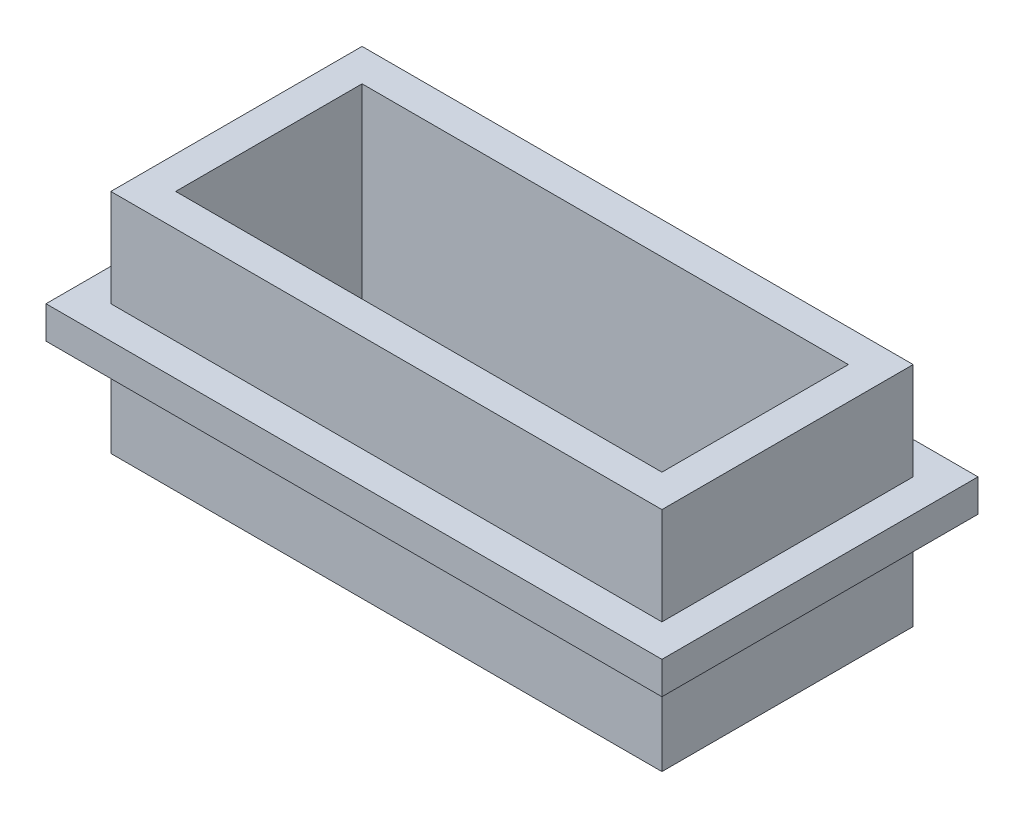
SolidWorks part; units mm, degrees
material "ABS"
ref_plane "Front Plane" through (0, 0, 0) normal (0, 0, 1) x (1, 0, 0)
ref_plane "Top Plane" through (0, 0, 0) normal (0, 1, 0) x (1, 0, 0)
ref_plane "Right Plane" through (0, 0, 0) normal (1, 0, 0) x (0, 0, -1)
sketch "Sketch1" plane through (0, 0, 0) normal (0, 1, 0) x (1, 0, 0)
  line L1 (-19.05, 7.3025) -> (19.05, 7.3025)
  line L2 (-19.05, 7.3025) -> (-19.05, -7.3025)
  line L3 (-19.05, -7.3025) -> (19.05, -7.3025)
  line L4 (19.05, 7.3025) -> (19.05, -7.3025)
  line L5 (-19.05, 7.3025) -> (19.05, -7.3025) construction
  line L6 (-19.05, -7.3025) -> (19.05, 7.3025) construction
  line L7 (-21.59, 9.8425) -> (21.59, 9.8425)
  line L8 (-21.59, 9.8425) -> (-21.59, -9.8425)
  line L9 (-21.59, -9.8425) -> (21.59, -9.8425)
  line L10 (21.59, 9.8425) -> (21.59, -9.8425)
  line L11 (-21.59, 9.8425) -> (21.59, -9.8425) construction
  line L12 (-21.59, -9.8425) -> (21.59, 9.8425) construction
  point P0 (0, 0)
  point P6 (0, 0)
  dimension "D1" = 38.1
  dimension "D2" = 14.605
  dimension "D3" = 2.54
  dimension "D4" = 2.54
extrude "Boss-Extrude1" add sketch "Sketch1" along normal blind 17.78
ref_plane "Plane1" through (0, 7.62, 0) normal (0, 1, 0) x (1, 0, 0)
sketch "Sketch2" plane through (0, 7.62, 0) normal (0, 1, 0) x (1, 0, 0)
  line L0 (-21.59, 9.8425) -> (-21.59, -9.8425) construction
  line L1 (-24.13, -12.3825) -> (24.13, -12.3825)
  line L2 (-24.13, -12.3825) -> (-24.13, 12.3825)
  line L3 (-24.13, 12.3825) -> (24.13, 12.3825)
  line L4 (24.13, -12.3825) -> (24.13, 12.3825)
  line L5 (-24.13, -12.3825) -> (24.13, 12.3825) construction
  line L6 (-24.13, 12.3825) -> (24.13, -12.3825) construction
  line L7 (21.59, 9.8425) -> (-21.59, 9.8425) construction
  line L9 (-19.05, -7.3025) -> (19.05, -7.3025)
  line L10 (-19.05, -7.3025) -> (-19.05, 7.3025)
  line L11 (-19.05, 7.3025) -> (19.05, 7.3025)
  line L12 (19.05, -7.3025) -> (19.05, 7.3025)
  line L13 (-19.05, -7.3025) -> (19.05, 7.3025) construction
  line L14 (-19.05, 7.3025) -> (19.05, -7.3025) construction
  point P0 (0, 0)
  point P10 (0, 0)
  dimension "D1" = 2.54
  dimension "D2" = 2.54
extrude "Boss-Extrude2" add sketch "Sketch2" along normal blind 2.54
